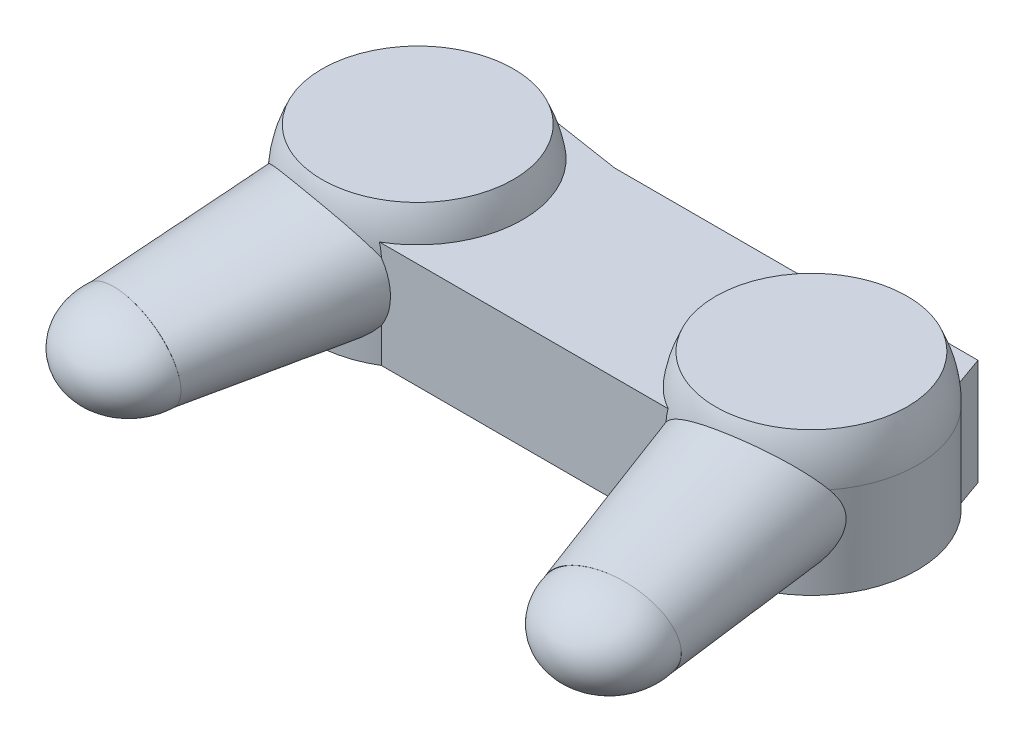
SolidWorks part; units mm, degrees
ref_plane "Plan de face" through (0, 0, 0) normal (0, 0, 1) x (1, 0, 0)
ref_plane "Plan de dessus" through (0, 0, 0) normal (0, 1, 0) x (1, 0, 0)
ref_plane "Plan de droite" through (0, 0, 0) normal (1, 0, 0) x (0, 0, -1)
sketch "Esquisse1" plane through (0, 0, 0) normal (0, 1, 0) x (1, 0, 0)
  line L0 (-30, 30) -> (-59.6471, 34.5882)
  line L5 (0, 30) -> (-30, 30)
  line L6 (0, 30) -> (0, -30)
  line L7 (0, -30) -> (-65, -30)
  line L8 (-65, 30) -> (-65, -30) construction
  line L9 (-65, 35) -> (-65, 30) construction
  line L10 (-30, 30) -> (-65, 30) construction
  line L11 (-65, 35) -> (-85, 35)
  line L13 (-65, -30) -> (-65, 0)
  line L14 (-65, 0) -> (-100, 0) construction
  line L15 (-85, 35) -> (-90, 20.8579)
  line L16 (-90, 20.8579) -> (-65, 0)
  line L17 (-90, 20.8579) -> (-65, 20.8579) construction
  arc A0 (-59.6471, 34.5882) -> (-65, 35) centre (-65, 0) ccw
  arc A1 (-65, 35) -> (-100, 0) centre (-65, 0) ccw construction
  point P4 (0, 0)
  dimension "D5" = 70
  dimension "D1" = 35
  dimension "D2" = 60
  dimension "D3" = 20
  dimension "D4" = 65
  dimension "D6" = 15
  dimension "D7" = 25
extrude "Boss.-Extru.1" add sketch "Esquisse1" along normal blind 35
sketch "Esquisse2" plane through (0, 0, 0) normal (0, 1, 0) x (1, 0, 0)
  line L2 (0, 0) -> (-65, 0) construction
  circle A0 centre (-65, 0) radius 35
  dimension "D1" = 70
  dimension "D2" = 65
extrude "Boss.-Extru.2" add sketch "Esquisse2" along normal blind 30
sketch "Esquisse3" plane through (0, 30, 0) normal (0, 1, 0) x (1, 0, 0)
  line L0 (-65, -35) -> (-65, 35)
  line L3 (-65, 0) -> (0, 0) construction
  arc A2 (-65, 35) -> (-65, -35) centre (-65, 0) cw
  dimension "D1" = 70
  dimension "D2" = 65
revolve "Révolution1" add sketch "Esquisse3" angle 180 about L0
sketch "Esquisse4" plane through (0, 0, 0) normal (0, -1, 0) x (1, 0, 0)
  circle A0 centre (-65, 0) radius 35
  dimension "D1" = 70
extrude "Enlèv. mat.-Extru.1" cut sketch "Esquisse4" against normal blind 33 from offset 45 offset against normal yes
sketch3d "Esquisse3D1"
  line L0 (0, 0, 0) -> (-65, 0, 0) construction
  line L1 (-65, 0, 0) -> (-78.8919, 0, 78.7846) construction
  line L2 (-65, 0, 0) -> (-65, 38.7204, 0) construction
  line L3 (-78.8919, 0, 78.7846) -> (-79.4454, 29.8301, 81.9241) construction
  line L4 (-65, 38.7204, 0) -> (-79.4454, 29.8301, 81.9241) construction
  line L5 (-78.8919, 0, 78.7846) -> (-64.1624, 0, 81.3818) construction
  line L6 (-65, 0, 0) -> (-53.2644, 0, 2.0693) construction
  line L7 (-65, 20, 0) -> (-56.9348, 20, 0) construction
  line L8 (-65, 20, 0) -> (-65, 20, -5.3806) construction
  line L9 (-79.1686, 14.9151, 80.3544) -> (-76.7799, 14.9151, 80.3544) construction
  dimension "D1" = 65
  dimension "D2" = 80
  dimension "D3" = 100
  dimension "D4" = 30
  dimension "D7" = 20
  dimension "D5" = 90
  dimension "D6" = 83.9
sketch3d "Esquisse3D5"
  line L0 (-78.8919, 0, 78.7846) -> (-64.1624, 0, 81.3818) construction
  line L1 (-78.8919, 0, 78.7846) -> (-79.4454, 29.8301, 81.9241) construction
sketch "Esquisse6" plane through (-15.6728, -9.6456, 88.8851) normal (-0.1727, -0.1063, 0.9792) x (0.9844, 0.0152, 0.1752)
  line L1 (-63.8571, 10.6756) -> (-48.9022, 10.4475) construction
  line L2 (-63.6284, 25.6738) -> (-43.6284, 25.6738) construction
  ellipse E0 centre (-63.6284, 25.6738) end of major axis (-43.6284, 25.6738) minor radius 15.0017
  dimension "D1" = 20
extrude "Boss.-Extru.3" add sketch "Esquisse6" against normal blind 70 draft 6 draft outward yes
sketch "Esquisse7" plane through (-15.6728, -9.6456, 88.8851) normal (-0.1727, -0.1063, 0.9792) x (0.985, -0.0164, 0.1719)
  line L0 (-44.4131, 23.9727) -> (-64.4104, 23.6435) construction
  line L1 (-64.1635, 8.6455) -> (-64.6573, 38.6415)
  line L2 (-64.1635, 8.6455) -> (-64.6573, 38.6415) construction
  ellipse E0 centre (-64.4104, 23.6435) end of major axis (-84.4077, 23.3143) minor radius 15 (-64.1635, 8.6455) -> (-64.6573, 38.6415) ccw
  dimension "D1" = 20
revolve "Révolution2" add sketch "Esquisse7" angle 180 about L1
ref_plane "Plan1" through (0, 20, 0) normal (0, 1, 0) x (1, 0, 0)
mirror "Symétrie3" about plane through (0, 35, -30) normal (-1, 0, 0) of bodies 106
split "Fractionner12" bodies to split 111
